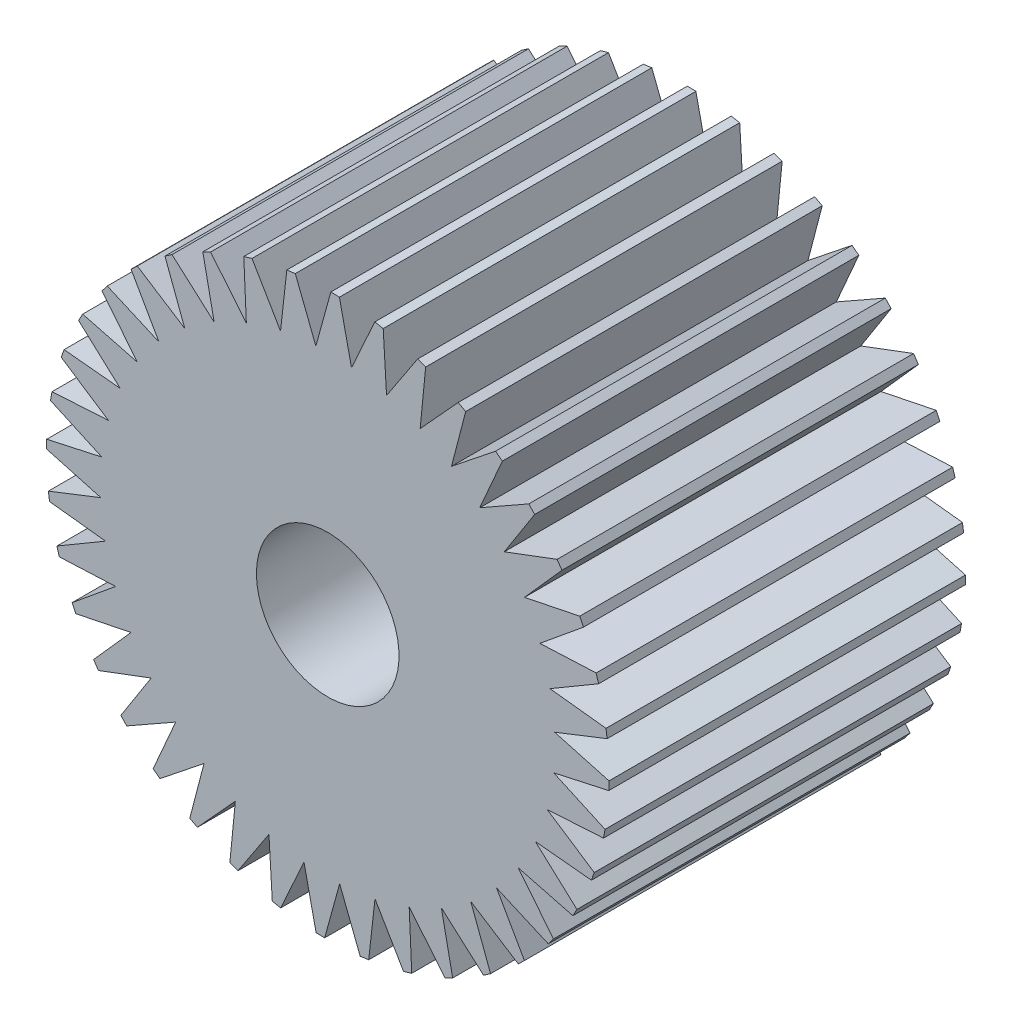
SolidWorks part; units mm, degrees
ref_plane "Front Plane" through (0, 0, 0) normal (0, 0, 1) x (1, 0, 0)
ref_plane "Top Plane" through (0, 0, 0) normal (0, 1, 0) x (1, 0, 0)
ref_plane "Right Plane" through (0, 0, 0) normal (1, 0, 0) x (0, 0, -1)
sketch "Sketch1" plane through (0, 0, 0) normal (0, 0, 1) x (1, 0, 0)
  line L0 (-6.6198, 31.1349) -> (-5.738, 38.993)
  line L1 (-4.5479, 39.1497) -> (-1.6625, 31.7875)
  line L2 (-5.738, 38.993) -> (-4.5479, 39.1497)
  line L3 (-1.6625, 31.7875) -> (0.4377, 39.4109)
  line L4 (0.4377, 39.4109) -> (1.6376, 39.3794)
  line L5 (1.6376, 39.3794) -> (3.3358, 31.6564)
  line L6 (3.3358, 31.6564) -> (6.6027, 38.8575)
  line L7 (6.6027, 38.8575) -> (7.7829, 38.6387)
  line L8 (7.7829, 38.6387) -> (8.252, 30.7451)
  line L9 (8.252, 30.7451) -> (12.6052, 37.3464)
  line L10 (12.6052, 37.3464) -> (13.7367, 36.9457)
  line L11 (13.7367, 36.9457) -> (12.9652, 29.076)
  line L12 (12.9652, 29.076) -> (18.2974, 34.915)
  line L13 (18.2974, 34.915) -> (19.3523, 34.3422)
  line L14 (19.3523, 34.3422) -> (17.3592, 26.6901)
  line L15 (17.3592, 26.6901) -> (23.5392, 31.6231)
  line L16 (23.5392, 31.6231) -> (24.4915, 30.8923)
  line L17 (24.4915, 30.8923) -> (21.3259, 23.6462)
  line L18 (21.3259, 23.6462) -> (28.2015, 27.5517)
  line L19 (28.2015, 27.5517) -> (29.0278, 26.6809)
  line L20 (29.0278, 26.6809) -> (24.7676, 20.0192)
  line L21 (24.7676, 20.0192) -> (32.1695, 22.8011)
  line L22 (32.1695, 22.8011) -> (32.8494, 21.8118)
  line L23 (32.8494, 21.8118) -> (27.5995, 15.8985)
  line L24 (27.5995, 15.8985) -> (35.3455, 17.4882)
  line L25 (35.3455, 17.4882) -> (35.8622, 16.4047)
  line L26 (35.8622, 16.4047) -> (29.7519, 11.3855)
  line L27 (29.7519, 11.3855) -> (37.6512, 11.7439)
  line L28 (37.6512, 11.7439) -> (37.9921, 10.593)
  line L29 (37.9921, 10.593) -> (31.1719, 6.5914)
  line L30 (31.1719, 6.5914) -> (39.03, 5.7096)
  line L31 (39.03, 5.7096) -> (39.1866, 4.5195)
  line L32 (39.1866, 4.5195) -> (31.8244, 1.6342)
  line L33 (31.8244, 1.6342) -> (39.4478, -0.466)
  line L34 (39.4478, -0.466) -> (39.4164, -1.666)
  line L35 (39.4164, -1.666) -> (31.6934, -3.3641)
  line L36 (31.6934, -3.3641) -> (38.8944, -6.631)
  line L37 (38.8944, -6.631) -> (38.6756, -7.8113)
  line L38 (38.6756, -7.8113) -> (30.7821, -8.2804)
  line L39 (30.7821, -8.2804) -> (37.3834, -12.6335)
  line L40 (37.3834, -12.6335) -> (36.9827, -13.765)
  line L41 (36.9827, -13.765) -> (29.1129, -12.9935)
  line L42 (29.1129, -12.9935) -> (34.952, -18.3258)
  line L43 (34.952, -18.3258) -> (34.3792, -19.3807)
  line L44 (34.3792, -19.3807) -> (26.727, -17.3876)
  line L45 (26.727, -17.3876) -> (31.66, -23.5676)
  line L46 (31.66, -23.5676) -> (30.9293, -24.5199)
  line L47 (30.9293, -24.5199) -> (23.6831, -21.3542)
  line L48 (23.6831, -21.3542) -> (27.5886, -28.2299)
  line L49 (27.5886, -28.2299) -> (26.7179, -29.0561)
  line L50 (26.7179, -29.0561) -> (20.0562, -24.7959)
  line L51 (20.0562, -24.7959) -> (22.838, -32.1979)
  line L52 (22.838, -32.1979) -> (21.8487, -32.8777)
  line L53 (21.8487, -32.8777) -> (15.9355, -27.6279)
  line L54 (15.9355, -27.6279) -> (17.5252, -35.3738)
  line L55 (17.5252, -35.3738) -> (16.4417, -35.8906)
  line L56 (16.4417, -35.8906) -> (11.4225, -29.7803)
  line L57 (11.4225, -29.7803) -> (11.7809, -37.6796)
  line L58 (11.7809, -37.6796) -> (10.6299, -38.0205)
  line L59 (10.6299, -38.0205) -> (6.6284, -31.2003)
  line L60 (6.6284, -31.2003) -> (5.7466, -39.0584)
  line L61 (5.7466, -39.0584) -> (4.5565, -39.215)
  line L62 (4.5565, -39.215) -> (1.6711, -31.8528)
  line L63 (1.6711, -31.8528) -> (-0.4291, -39.4762)
  line L64 (-0.4291, -39.4762) -> (-1.629, -39.4447)
  line L65 (-1.629, -39.4447) -> (-3.3272, -31.7218)
  line L66 (-3.3272, -31.7218) -> (-6.5941, -38.9228)
  line L67 (-6.5941, -38.9228) -> (-7.7743, -38.704)
  line L68 (-7.7743, -38.704) -> (-8.2434, -30.8105)
  line L69 (-8.2434, -30.8105) -> (-12.5966, -37.4118)
  line L70 (-12.5966, -37.4118) -> (-13.7281, -37.011)
  line L71 (-13.7281, -37.011) -> (-12.9566, -29.1413)
  line L72 (-12.9566, -29.1413) -> (-18.2888, -34.9803)
  line L73 (-18.2888, -34.9803) -> (-19.3437, -34.4076)
  line L74 (-19.3437, -34.4076) -> (-17.3506, -26.7554)
  line L75 (-17.3506, -26.7554) -> (-23.5306, -31.6884)
  line L76 (-23.5306, -31.6884) -> (-24.4829, -30.9576)
  line L77 (-24.4829, -30.9576) -> (-21.3173, -23.7115)
  line L78 (-21.3173, -23.7115) -> (-28.1929, -27.617)
  line L79 (-28.1929, -27.617) -> (-29.0192, -26.7463)
  line L80 (-29.0192, -26.7463) -> (-24.759, -20.0845)
  line L81 (-24.759, -20.0845) -> (-32.1609, -22.8664)
  line L82 (-32.1609, -22.8664) -> (-32.8408, -21.8771)
  line L83 (-32.8408, -21.8771) -> (-27.5909, -15.9638)
  line L84 (-27.5909, -15.9638) -> (-35.3369, -17.5535)
  line L85 (-35.3369, -17.5535) -> (-35.8536, -16.4701)
  line L86 (-35.8536, -16.4701) -> (-29.7433, -11.4509)
  line L87 (-29.7433, -11.4509) -> (-37.6426, -11.8092)
  line L88 (-37.6426, -11.8092) -> (-37.9835, -10.6583)
  line L89 (-37.9835, -10.6583) -> (-31.1633, -6.6567)
  line L90 (-31.1633, -6.6567) -> (-39.0214, -5.775)
  line L91 (-39.0214, -5.775) -> (-39.178, -4.5848)
  line L92 (-39.178, -4.5848) -> (-31.8158, -1.6995)
  line L93 (-31.8158, -1.6995) -> (-39.4392, 0.4007)
  line L94 (-39.4392, 0.4007) -> (-39.4078, 1.6007)
  line L95 (-39.4078, 1.6007) -> (-31.6848, 3.2988)
  line L96 (-31.6848, 3.2988) -> (-38.8858, 6.5657)
  line L97 (-38.8858, 6.5657) -> (-38.667, 7.746)
  line L98 (-38.667, 7.746) -> (-30.7735, 8.215)
  line L99 (-30.7735, 8.215) -> (-37.3748, 12.5682)
  line L100 (-37.3748, 12.5682) -> (-36.9741, 13.6997)
  line L101 (-36.9741, 13.6997) -> (-29.1044, 12.9282)
  line L102 (-29.1044, 12.9282) -> (-34.9434, 18.2605)
  line L103 (-34.9434, 18.2605) -> (-34.3706, 19.3153)
  line L104 (-34.3706, 19.3153) -> (-26.7184, 17.3222)
  line L105 (-26.7184, 17.3222) -> (-31.6515, 23.5023)
  line L106 (-31.6515, 23.5023) -> (-30.9207, 24.4546)
  line L107 (-30.9207, 24.4546) -> (-23.6745, 21.2889)
  line L108 (-23.6745, 21.2889) -> (-27.58, 28.1646)
  line L109 (-27.58, 28.1646) -> (-26.7093, 28.9908)
  line L110 (-26.7093, 28.9908) -> (-20.0476, 24.7306)
  line L111 (-20.0476, 24.7306) -> (-22.8294, 32.1325)
  line L112 (-22.8294, 32.1325) -> (-21.8401, 32.8124)
  line L113 (-21.8401, 32.8124) -> (-15.9269, 27.5625)
  line L114 (-15.9269, 27.5625) -> (-17.5166, 35.3085)
  line L115 (-17.5166, 35.3085) -> (-16.4331, 35.8253)
  line L116 (-16.4331, 35.8253) -> (-11.4139, 29.715)
  line L117 (-11.4139, 29.715) -> (-11.7723, 37.6143)
  line L118 (-11.7723, 37.6143) -> (-10.6213, 37.9552)
  line L119 (-10.6213, 37.9552) -> (-6.6198, 31.1349)
  point P2 (0, 0)
  point P164 (0.0043, -0.0327)
  dimension "D1" = 5
  dimension "D2" = 40
extrude "Boss-Extrude1" add sketch "Sketch1" along normal blind 50
sketch "Sketch2" plane through (0, 0, 0) normal (0, 0, -1) x (-1, 0, 0)
  circle A0 centre (0, 0) radius 10
extrude "Cut-Extrude1" cut sketch "Sketch2" against normal blind 50
